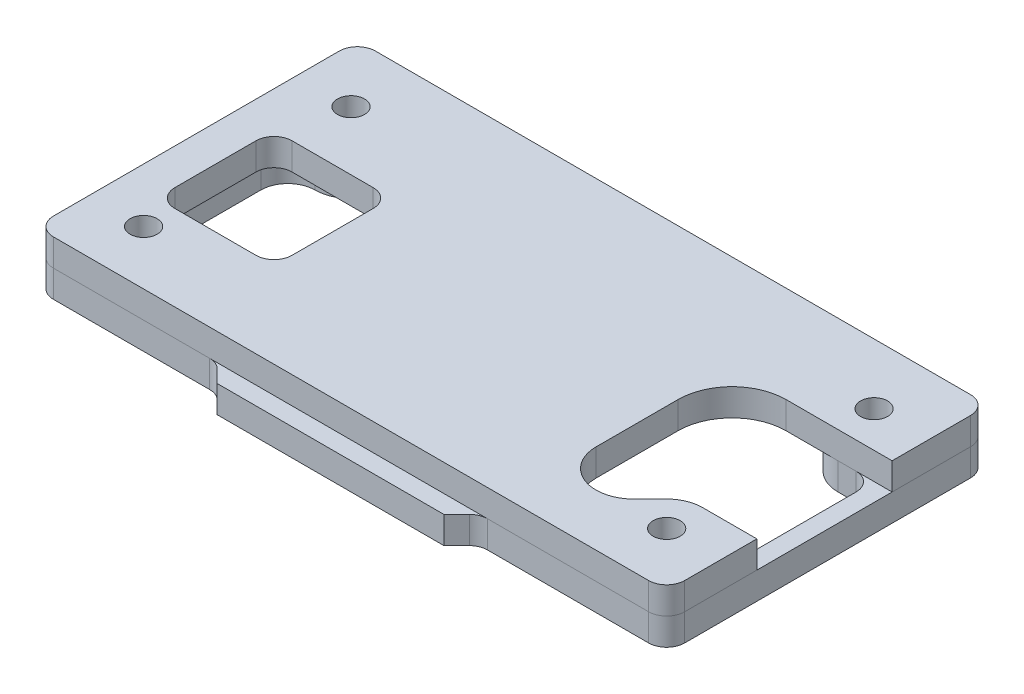
SolidWorks part; units mm, degrees
ref_plane "Front Plane" through (0, 0, 0) normal (0, 0, 1) x (1, 0, 0)
ref_plane "Top Plane" through (0, 0, 0) normal (0, 1, 0) x (1, 0, 0)
ref_plane "Right Plane" through (0, 0, 0) normal (1, 0, 0) x (0, 0, -1)
sketch "Sketch1" plane through (0, 0, 0) normal (0, 1, 0) x (1, 0, 0)
  line L0 (-35, 17.85) -> (35, 17.85)
  line L1 (-32.5, -15.35) -> (32.5, -15.35) construction
  line L2 (-32.5, -15.35) -> (-32.5, 15.35) construction
  line L3 (-32.5, 15.35) -> (32.5, 15.35) construction
  line L4 (32.5, -15.35) -> (32.5, 15.35) construction
  line L5 (0, 15.35) -> (0, -15.35) construction
  line L6 (-32.5, 0) -> (32.5, 0) construction
  line L11 (35, -17.85) -> (35, 17.85)
  line L12 (-35, -17.85) -> (35, -17.85)
  line L13 (-35, -17.85) -> (-35, 17.85)
  line L15 (-29, -11.85) -> (29, -11.85) construction
  line L16 (-29, -11.85) -> (-29, 11.15) construction
  line L17 (-29, 11.15) -> (29, 11.15) construction
  line L18 (29, -11.85) -> (29, 11.15) construction
  line L19 (0, 11.15) -> (0, -11.85) construction
  line L20 (-29, -0.35) -> (29, -0.35) construction
  circle A0 centre (-29, -11.85) radius 1.5
  circle A1 centre (29, -11.85) radius 1.5
  circle A2 centre (29, 11.15) radius 1.5
  circle A3 centre (-29, 11.15) radius 1.5
  point P0 (0, 0)
  point P8 (0, -0.35)
  dimension "D4" = 3
  dimension "D1" = 65
  dimension "D2" = 30.7
  dimension "D5" = 3.5
  dimension "D6" = 4.2
  dimension "D7" = 3.5
  dimension "D8" = 23
  dimension "D9" = 58
  dimension "D3" = 2.5
extrude "Boss-Extrude1" add sketch "Sketch1" along normal blind 3
sketch "Sketch2" plane through (0, 3, 0) normal (0, 1, 0) x (1, 0, 0)
  line L0 (-18, -8.39) -> (-31, -8.39)
  line L1 (-19.5, -6.89) -> (-29.5, -6.89) construction
  line L2 (-19.5, -6.89) -> (-19.5, 3.11) construction
  line L3 (-19.5, 3.11) -> (-29.5, 3.11) construction
  line L4 (-29.5, -6.89) -> (-29.5, 3.11) construction
  line L5 (-24.5, 3.11) -> (-24.5, -6.89) construction
  line L6 (-19.5, -1.89) -> (-29.5, -1.89) construction
  line L7 (-31, -8.39) -> (-31, 4.61)
  line L8 (-18, 4.61) -> (-31, 4.61)
  line L9 (-18, -8.39) -> (-18, 4.61)
  line L10 (-32.5, -15.35) -> (32.5, -15.35) construction
  line L11 (-32.5, -15.35) -> (-32.5, 15.35) construction
  line L12 (32.5, -15.35) -> (32.5, 15.35) construction
  line L13 (17.25, 1.15) -> (17.25, -7.9341)
  line L14 (24.3274, -10.8657) -> (26.1716, -9.0216)
  line L15 (29, -7.85) -> (35, -7.85)
  line L16 (35, -7.85) -> (35, 7.15)
  line L17 (35, 7.15) -> (23.25, 7.15)
  line L18 (35, -17.85) -> (35, 17.85) construction
  circle A0 centre (21.25, -6.08) radius 3 construction
  circle A1 centre (28.59, 0.4) radius 3 construction
  circle A2 centre (29, -11.85) radius 4 construction
  circle A3 centre (29, -11.85) radius 1.5 construction
  arc A4 (24.3274, -10.8657) -> (17.25, -7.9341) centre (21.3959, -7.9341) cw
  circle A5 centre (29, 11.15) radius 4 construction
  circle A6 centre (29, 11.15) radius 1.5 construction
  arc A7 (29, -7.85) -> (26.1716, -9.0216) centre (29, -11.85) ccw
  arc A8 (23.25, 7.15) -> (17.25, 1.15) centre (23.25, 1.15) ccw
  point P0 (-24.5, -1.89)
  point P20 (18.25, -6.08)
  point P25 (21.3959, -12.08)
  point P28 (21.25, -9.08)
  dimension "D9" = 6
  dimension "D11" = 8
  dimension "D14" = 6
  dimension "D2" = 10
  dimension "D3" = 13.46
  dimension "D4" = 8
  dimension "D5" = 15.75
  dimension "D6" = 3.91
  dimension "D7" = 11.25
  dimension "D8" = 9.27
  dimension "D10" = 1
  dimension "D12" = 45
  dimension "D13" = 3
  dimension "D1" = 1.5
extrude "Cut-Extrude1" cut sketch "Sketch2" against normal through all
fillet "Fillet1" radius 2 4 edges at (-18, 1.5, 8.39) (-31, 1.5, 8.39) (-18, 1.5, -4.61) (-31, 1.5, -4.61)
fillet "Fillet2" radius 2 4 edges at (35, 1.5, -17.85) (35, 1.5, 17.85) (-35, 1.5, 17.85) (-35, 1.5, -17.85)
sketch "Sketch3" plane through (0, 0, 0) normal (0, -1, 0) x (1, 0, 0)
  line L0 (29, 7.85) -> (35, 7.85) construction
  line L1 (35, 15.85) -> (35, 7.85) construction
  line L2 (35, -7.15) -> (35, -15.85) construction
  line L3 (33, -17.85) -> (-33, -17.85) construction
  line L4 (-35, -15.85) -> (-35, 15.85) construction
  line L5 (29, 7.85) -> (35, 7.85) construction
  line L6 (35, 15.85) -> (35, 7.85)
  line L7 (35, -7.15) -> (35, -15.85)
  line L8 (33, -17.85) -> (-33, -17.85)
  line L9 (-35, -15.85) -> (-35, 15.85)
  line L10 (29, 7.85) -> (31, 7.85)
  line L11 (35, -7.15) -> (35, 7.85)
  line L12 (33, 5.85) -> (33, -5.15)
  line L13 (25, 11.85) -> (25, 17.85)
  line L14 (25, 17.85) -> (33, 17.85)
  line L15 (35, -7.15) -> (23.25, -7.15) construction
  line L16 (29, -7.15) -> (31, -7.15)
  line L18 (25, -11.15) -> (25, -12.85)
  line L19 (23, -14.85) -> (-23, -14.85)
  line L20 (-25, -11.15) -> (-25, -12.85)
  line L21 (-32, 6.39) -> (-32, -4.15)
  line L22 (-18, 8.39) -> (-31, 8.39) construction
  line L23 (-29, 8.39) -> (-30, 8.39)
  line L24 (-25.54, 11.85) -> (-25.54, 17.85)
  line L25 (-33, 17.85) -> (-25.54, 17.85)
  arc A0 (26.1716, 9.0216) -> (29, 7.85) centre (29, 11.85) ccw construction
  arc A1 (35, 15.85) -> (33, 17.85) centre (33, 15.85) ccw construction
  arc A2 (33, -17.85) -> (35, -15.85) centre (33, -15.85) ccw construction
  arc A3 (-35, -15.85) -> (-33, -17.85) centre (-33, -15.85) ccw construction
  arc A4 (-33, 17.85) -> (-35, 15.85) centre (-33, 15.85) ccw construction
  arc A5 (26.1716, 9.0216) -> (29, 7.85) centre (29, 11.85) ccw
  arc A6 (35, 15.85) -> (33, 17.85) centre (33, 15.85) ccw
  arc A7 (33, -17.85) -> (35, -15.85) centre (33, -15.85) ccw
  arc A8 (-35, -15.85) -> (-33, -17.85) centre (-33, -15.85) ccw
  arc A9 (-33, 17.85) -> (-35, 15.85) centre (-33, 15.85) ccw
  circle A10 centre (29, 11.85) radius 4 construction
  circle A11 centre (29, 11.85) radius 1.5 construction
  arc A12 (26.1716, 9.0216) -> (25, 11.85) centre (29, 11.85) cw
  arc A13 (31, 7.85) -> (33, 5.85) centre (31, 5.85) cw
  circle A14 centre (29, -11.15) radius 4 construction
  circle A15 centre (29, -11.15) radius 1.5 construction
  arc A17 (33, -5.15) -> (31, -7.15) centre (31, -5.15) cw
  arc A18 (25, -12.85) -> (23, -14.85) centre (23, -12.85) cw
  arc A19 (29, -7.15) -> (25, -11.15) centre (29, -11.15) ccw
  circle A20 centre (-29, -11.15) radius 4 construction
  circle A21 centre (-29, -11.15) radius 1.5 construction
  arc A22 (-23, -14.85) -> (-25, -12.85) centre (-23, -12.85) cw
  arc A23 (-32, -4.15) -> (-29, -7.15) centre (-29, -4.15) ccw
  arc A24 (-29, -7.15) -> (-25, -11.15) centre (-29, -11.15) cw
  circle A25 centre (-29, 11.85) radius 3.46 construction
  circle A26 centre (-29, 11.85) radius 1.5 construction
  arc A27 (-30, 8.39) -> (-32, 6.39) centre (-30, 6.39) ccw
  arc A28 (-29, 8.39) -> (-25.54, 11.85) centre (-29, 11.85) ccw
  circle A29 centre (-29, 11.85) radius 1.5
  circle A30 centre (-29, -11.15) radius 1.5
  circle A31 centre (29, -11.15) radius 1.5
  circle A32 centre (29, 11.85) radius 1.5
  point P71 (0, 0)
  point P72 (0, 0)
  dimension "D2" = 2
  dimension "D4" = 2
  dimension "D6" = 2
  dimension "D1" = 2
  dimension "D3" = 3
  dimension "D5" = 3
extrude "Boss-Extrude2" add sketch "Sketch3" along normal blind 3 separate body
sketch "Sketch4" plane through (0, 0, 0) normal (0, 1, 0) x (1, 0, 0)
  line L0 (-25.54, -15.85) -> (-9.77, -15.85)
  line L1 (-9.77, -15.85) -> (-7.77, -17.85)
  line L2 (-7.77, -17.85) -> (7.23, -17.85)
  line L3 (7.23, -17.85) -> (9.23, -15.85)
  line L4 (9.23, -15.85) -> (25, -15.85)
  line L5 (-25.54, -15.85) -> (-25.54, -17.85)
  line L6 (-25.54, -17.85) -> (-14.8411, -17.85)
  line L7 (-14.8411, -17.85) -> (-12.8411, -19.85)
  line L8 (-12.8411, -19.85) -> (12.3011, -19.85)
  line L9 (12.3011, -19.85) -> (14.3011, -17.85)
  line L10 (14.3011, -17.85) -> (25, -17.85)
  line L11 (25, -17.85) -> (25, -15.85)
  point P2 (0, 0)
  point P13 (0, 0)
  point P14 (-12.0274, -16.914)
  point P16 (-8.8813, -18.0418)
  point P18 (-5.3686, -17.489)
  point P19 (9.2779, -17.6371)
  point P20 (0, 0)
  point P21 (6.6649, -19.0199)
  point P22 (-11.6881, -19.85)
  dimension "D1" = 2
  dimension "D2" = 5
  dimension "D3" = 2
  dimension "D4" = 15
extrude "Boss-Extrude3" add sketch "Sketch4" against normal up to surface (3 mm away) up to face at (1.1242, -3, -0.1812)
fillet "Fillet3" radius 2 2 edges at (-25.54, -1.5, 15.85) (25, -1.5, 15.85)
fillet "Fillet4" radius 2 4 edges at (-14.8411, -1.5, 17.85) (14.3011, -1.5, 17.85) (7.23, -1.5, 17.85) (-7.77, -1.5, 17.85)
